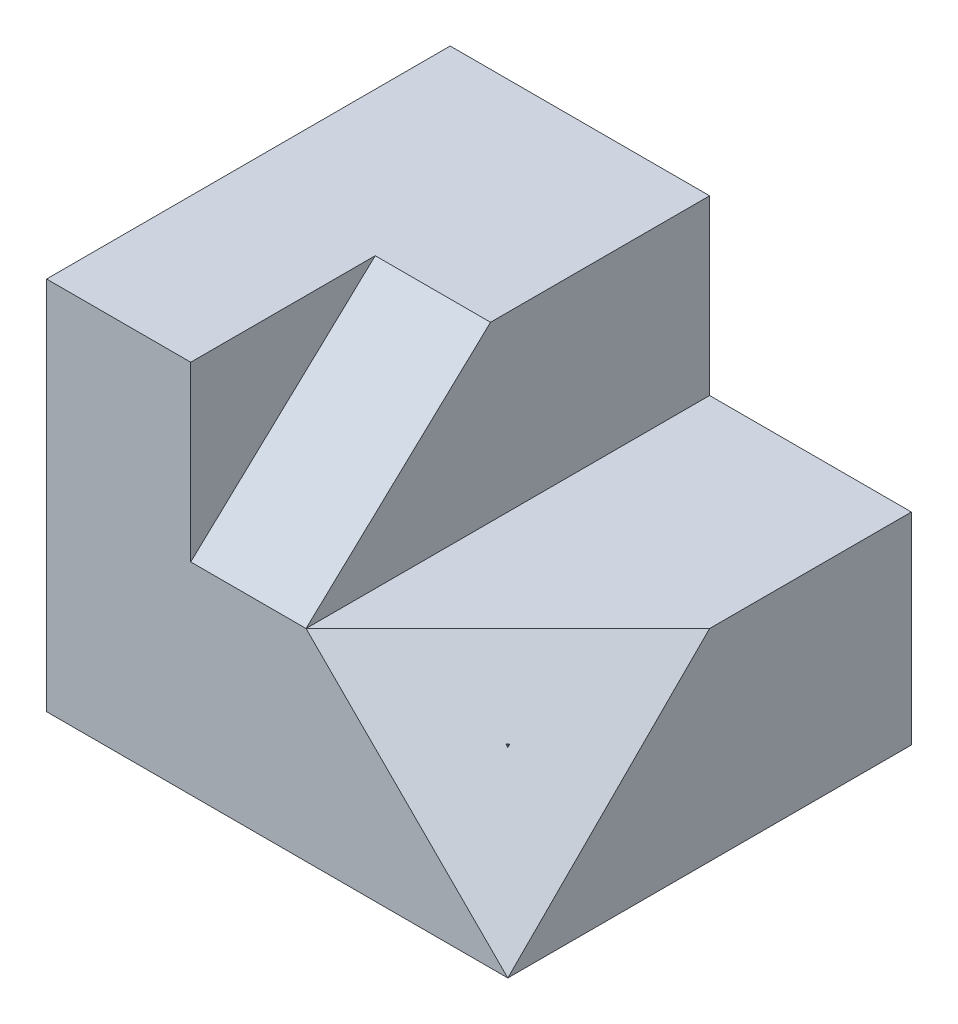
SolidWorks part; units mm, degrees
ref_plane "Front Plane" through (0, 0, 0) normal (0, 0, 1) x (1, 0, 0)
ref_plane "Top Plane" through (0, 0, 0) normal (0, 1, 0) x (1, 0, 0)
ref_plane "Right Plane" through (0, 0, 0) normal (1, 0, 0) x (0, 0, -1)
sketch "Sketch2" plane through (0, 0, 0) normal (0, 1, 0) x (1, 0, 0)
  line L1 (40, -35) -> (-40, -35)
  line L2 (40, -35) -> (40, 35)
  line L3 (40, 35) -> (-40, 35)
  line L4 (-40, -35) -> (-40, 35)
  line L5 (40, -35) -> (-40, 35) construction
  line L6 (40, 35) -> (-40, -35) construction
  point P0 (0, 0)
  dimension "D1" = 80
  dimension "D2" = 70
extrude "Boss-Extrude1" add sketch "Sketch2" along normal blind 65
sketch "Sketch3" plane through (40, 0, 0) normal (1, 0, 0) x (0, 0, -1)
  line L0 (35, 65) -> (35, 0) construction
  line L1 (-35, 65) -> (35, 65)
  line L2 (-35, 65) -> (-35, 35)
  line L3 (-35, 35) -> (35, 35)
  line L4 (35, 65) -> (35, 35)
  line L5 (-35, 0) -> (35, 0) construction
  dimension "D1" = 35
extrude "Cut-Extrude1" cut sketch "Sketch3" against normal blind 35
sketch "Sketch4" plane through (5, 0, 0) normal (1, 0, 0) x (0, 0, -1)
  line L0 (-35, 35) -> (-3, 65)
  line L1 (35, 65) -> (-35, 65) construction
  line L2 (-35, 35) -> (-35, 65)
  line L3 (-35, 65) -> (-3, 65)
  dimension "D1" = 38
  dimension "D2" = 30
  dimension "D3" = 35
extrude "Boss-Extrude2" add sketch "Sketch4" against normal blind 20
sketch "Sketch5" plane through (5, 0, 0) normal (1, 0, 0) x (0, 0, -1)
  line L0 (-35, 35) -> (-3, 65)
  line L1 (35, 65) -> (-35, 65) construction
  line L2 (-3, 65) -> (-35, 65)
  line L3 (-35, 65) -> (-35, 35)
  dimension "D1" = 38
  dimension "D2" = 30
  dimension "D3" = 35
extrude "Cut-Extrude2" cut sketch "Sketch5" against normal blind 20
sketch3d "3DSketch1"
  line L0 (40, 0, 35) -> (40, 35, 0)
  line L1 (40, 35, 35) -> (40, 35, -35) construction
  line L2 (40, 35, 0) -> (5, 35, 35)
  line L3 (5, 35, 35) -> (40, 0, 35)
  point P7 (0, 0, 0)
  dimension "D1" = 35
ref_plane "Plane2" through (25, 25, 25) normal (-0.5774, -0.5774, -0.5774) x (-0.8165, 0.4082, 0.4082)
sketch "Sketch6" plane through (25, 25, 25) normal (-0.5774, -0.5774, -0.5774) x (-0.8165, 0.4082, 0.4082)
  line L0 (-18.3712, -24.7487) -> (-18.3712, 24.7487) construction
  line L1 (24.4949, 0) -> (-18.3712, -24.7487) construction
  line L2 (-18.3712, 24.7487) -> (24.4949, 0) construction
  line L3 (-18.3712, -24.7487) -> (-18.3712, 24.7487)
  line L4 (24.4949, 0) -> (-18.3712, -24.7487)
  line L5 (-18.3712, 24.7487) -> (24.4949, 0)
extrude "Cut-Extrude3" cut sketch "Sketch6" against normal blind 20
